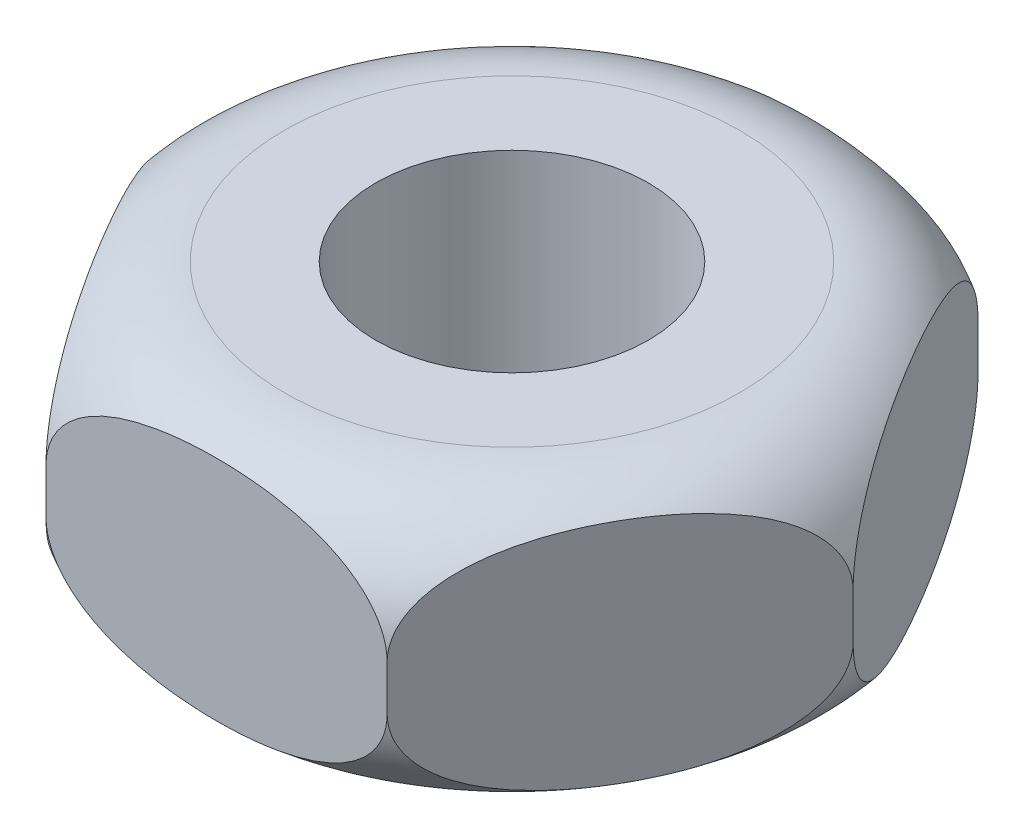
SolidWorks part; units mm, degrees
ref_plane "Front Plane" through (0, 0, 0) normal (0, 0, 1) x (1, 0, 0)
ref_plane "Top Plane" through (0, 0, 0) normal (0, 1, 0) x (1, 0, 0)
ref_plane "Right Plane" through (0, 0, 0) normal (1, 0, 0) x (0, 0, -1)
sketch "Sketch1" plane through (0, 0, 0) normal (0, 1, 0) x (1, 0, 0)
  line L1 (15.0111, 0) -> (7.5056, 13)
  line L2 (7.5056, 13) -> (-7.5056, 13)
  line L3 (-7.5056, 13) -> (-15.0111, 0)
  line L4 (-15.0111, 0) -> (-7.5056, -13)
  line L5 (-7.5056, -13) -> (7.5056, -13)
  line L6 (7.5056, -13) -> (15.0111, 0)
  circle A0 centre (0, 0) radius 13 construction
  circle A1 centre (0, 0) radius 6
  dimension "D2" = 12
  dimension "D1" = 26
extrude "Boss-Extrude1" add sketch "Sketch1" along normal mid plane 12
sketch "Sketch3" plane through (0, 0, 0) normal (0, 0, 1) x (1, 0, 0)
  line L5 (10.0111, 6) -> (15.0111, 6)
  line L6 (0, 1.1648) -> (0, 10.8352) construction
  line L7 (15.0111, 6) -> (15.0111, 1)
  arc A0 (15.0111, 1) -> (10.0111, 6) centre (10.0111, 1) ccw
  point P16 (0, 6)
  dimension "D1" = 5
revolve "Cut-Revolve1" cut sketch "Sketch3" angle 360 about L6
mirror "Mirror1" about plane through (0, 0, 0) normal (0, 1, 0) of "Cut-Revolve1"
